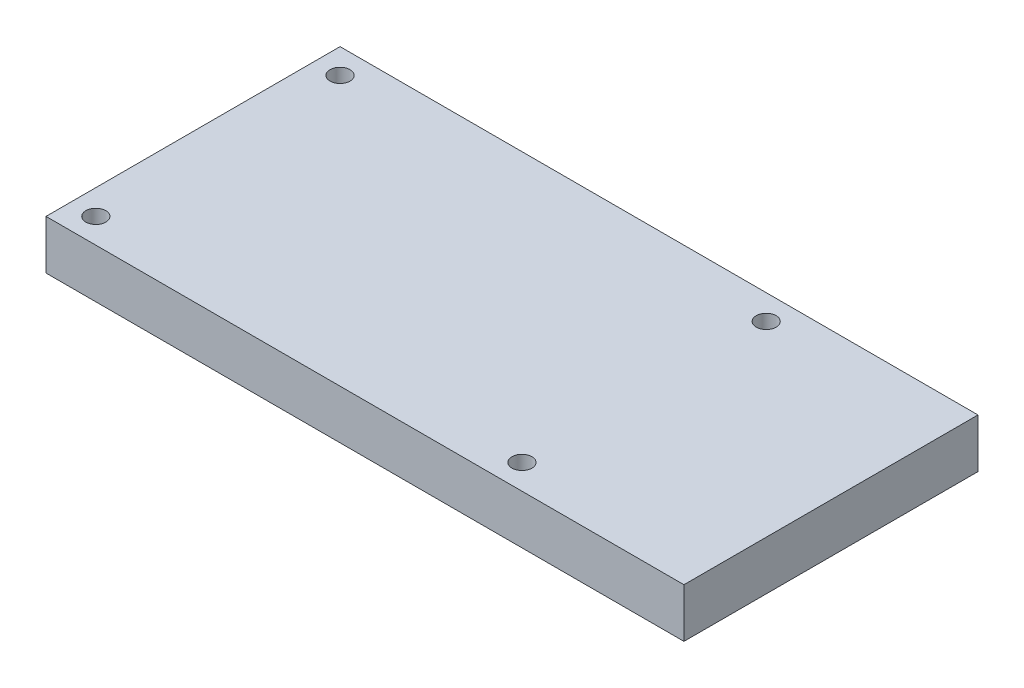
SolidWorks part; units mm, degrees
ref_plane "Front Plane" through (0, 0, 0) normal (0, 0, 1) x (1, 0, 0)
ref_plane "Top Plane" through (0, 0, 0) normal (0, 1, 0) x (1, 0, 0)
ref_plane "Right Plane" through (0, 0, 0) normal (1, 0, 0) x (0, 0, -1)
sketch "Sketch1" plane through (0, 0, 0) normal (0, 1, 0) x (1, 0, 0)
  line L0 (0, 14.986) -> (0, -14.986) construction
  line L1 (-32.512, -14.986) -> (32.512, -14.986)
  line L2 (-32.512, -14.986) -> (-32.512, 14.986)
  line L3 (-32.512, 14.986) -> (32.512, 14.986)
  line L4 (32.512, -14.986) -> (32.512, 14.986)
  line L5 (-32.512, -14.986) -> (32.512, 14.986) construction
  line L6 (-32.512, 14.986) -> (32.512, -14.986) construction
  line L7 (-32.512, 0) -> (32.512, 0) construction
  circle A0 centre (-29.972, 12.446) radius 1.016
  circle A1 centre (-29.972, -12.446) radius 1.016
  circle A2 centre (13.462, 12.446) radius 1.016
  circle A3 centre (13.462, -12.446) radius 1.016
  point P0 (0, 0)
  dimension "D5" = 19.05
  dimension "D6" = 2.032
  dimension "D7" = 2.032
  dimension "D1" = 65.024
  dimension "D2" = 29.972
  dimension "D3" = 2.54
  dimension "D4" = 2.54
extrude "Boss-Extrude1" add sketch "Sketch1" along normal blind 5.0038
